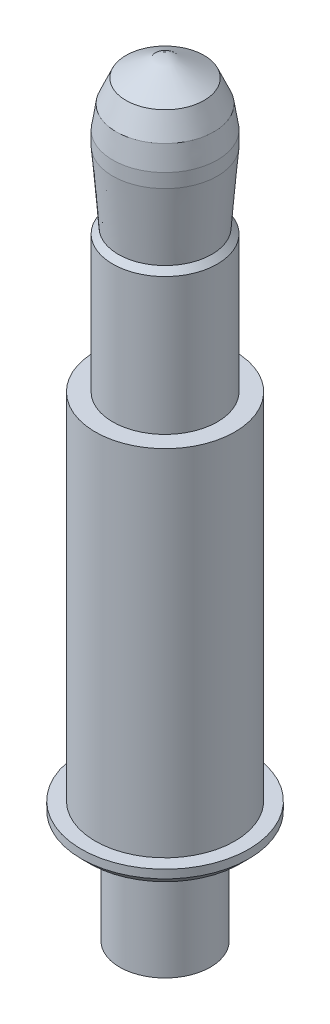
SolidWorks part; units mm, degrees
ref_plane "Alzado" through (0, 0, 0) normal (0, 0, 1) x (1, 0, 0)
ref_plane "Planta" through (0, 0, 0) normal (0, 1, 0) x (1, 0, 0)
ref_plane "Vista lateral" through (0, 0, 0) normal (1, 0, 0) x (0, 0, -1)
ref_plane "Plane1" through (0, 0, 0) normal (0, 0, -1) x (-1, 0, 0)
sketch "Sketch1" plane through (0, 0, 0) normal (0, 0, -1) x (-1, 0, 0)
  line L0 (-998.7639, 0.75) -> (49001.2361, 0.75) construction
  line L1 (0, -1000) -> (0, 49000) construction
  line L2 (0, 5.52) -> (-0.28, 5.3583)
  line L3 (-0.28, 5.3583) -> (-0.35, 5.1983)
  line L4 (-0.35, 5.1983) -> (-0.375, 5.0358)
  line L5 (-0.375, 5.0358) -> (-0.375, 4.9358)
  line L6 (-0.375, 4.9358) -> (-0.335, 4.43)
  line L7 (-0.335, 4.43) -> (-0.375, 4.39)
  line L8 (-0.375, 4.39) -> (-0.375, 3.41)
  line L9 (-0.375, 3.41) -> (-0.5, 3.41)
  line L10 (-0.5, 3.41) -> (-0.5, 0.87)
  line L11 (-0.5, 0.87) -> (-0.6, 0.87)
  line L12 (-0.6, 0.87) -> (-0.6, 0.75)
  line L13 (-998.7539, -0.022) -> (49001.2461, -0.022) construction
  line L14 (-1000, 0) -> (49000, 0) construction
  line L15 (-1000, 5.52) -> (49000, 5.52) construction
  line L16 (-1000.28, 5.3583) -> (48999.72, 5.3583) construction
  line L17 (-1000.35, 5.1983) -> (48999.65, 5.1983) construction
  line L18 (-1000.375, 5.0358) -> (48999.625, 5.0358) construction
  line L19 (-1000.375, 4.9358) -> (48999.625, 4.9358) construction
  line L20 (-1000.335, 4.43) -> (48999.665, 4.43) construction
  line L21 (-1000.375, 4.39) -> (48999.625, 4.39) construction
  line L22 (-1000.375, 3.41) -> (48999.625, 3.41) construction
  line L23 (-1000.5, 0.87) -> (48999.5, 0.87) construction
  line L24 (-0.28, -994.6417) -> (-0.28, 49005.3583) construction
  line L25 (-0.35, -994.8017) -> (-0.35, 49005.1983) construction
  line L26 (-0.375, -994.9642) -> (-0.375, 49005.0358) construction
  line L27 (-0.335, -995.57) -> (-0.335, 49004.43) construction
  line L28 (-0.5, -996.59) -> (-0.5, 49003.41) construction
  line L29 (-0.6, -997.33) -> (-0.6, 49002.67) construction
  line L30 (-0.325, -994.1128) -> (-0.325, 49005.8872) construction
  line L31 (-0.325, 0.75) -> (-0.6, 0.75)
  line L32 (-0.325, 0.75) -> (-0.325, 0)
  line L33 (0, -0.022) -> (-0.325, 0)
  line L34 (0, -0.022) -> (0, 5.52)
  point P52 (-0.325, 0)
  point P54 (0, -0.022)
  dimension "D1" = 3.41
  dimension "D2" = 4.39
  dimension "D3" = 4.43
  dimension "D4" = 5.0358
  dimension "D5" = 4.9358
  dimension "D6" = 5.1983
  dimension "D7" = 5.3583
  dimension "D8" = 5.52
  dimension "D9" = 0.28
  dimension "D10" = 0.335
  dimension "D11" = 0.35
  dimension "D12" = 0.375
  dimension "D13" = 0.5
  dimension "D14" = 0.6
  dimension "D15" = 0.87
  dimension "D16" = 0.75
  dimension "D17" = 0.022
  dimension "D18" = 0.325
revolve "Revolve1" add sketch "Sketch1" angle 360 about L1
chamfer "Chamfer1" distance 0.06 angle 45 1 edges at (0.6, 0.75, 0)
